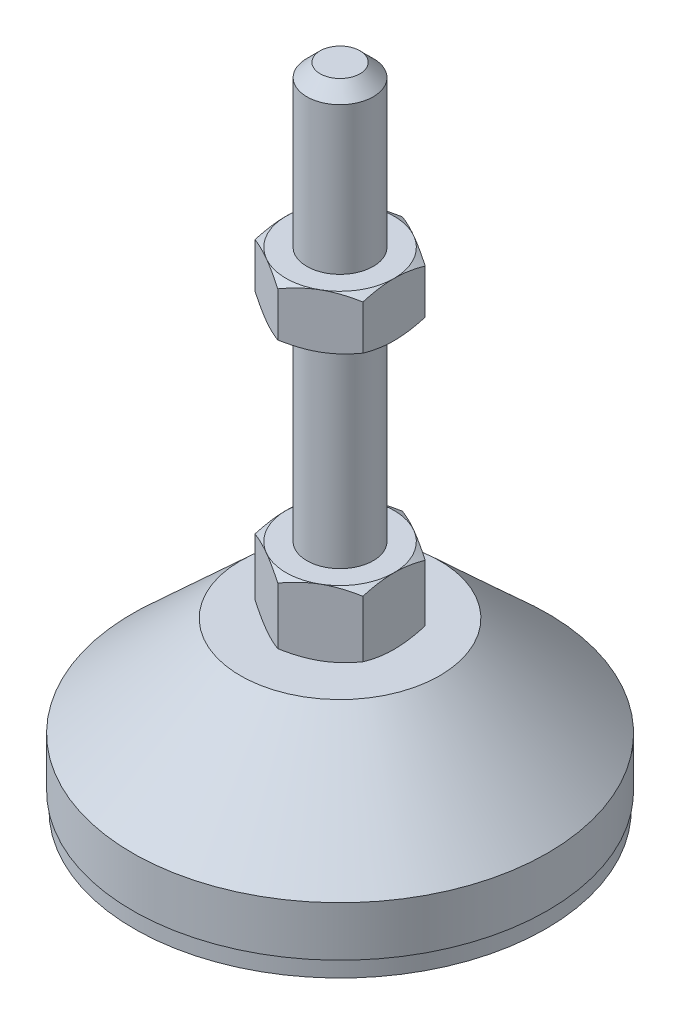
SolidWorks part; units mm, degrees
ref_plane "Спереди" through (0, 0, 0) normal (0, 0, 1) x (1, 0, 0)
ref_plane "Сверху" through (0, 0, 0) normal (0, 1, 0) x (1, 0, 0)
ref_plane "Справа" through (0, 0, 0) normal (1, 0, 0) x (0, 0, -1)
sketch "Эскиз1" plane through (0, 0, 0) normal (0, 0, 1) x (1, 0, 0)
  line L0 (0, 0) -> (-24.8, 0)
  line L1 (-24.8, 0) -> (-24.8, 2)
  line L2 (-24.8, 2) -> (-25, 2)
  line L3 (-25, 2) -> (-25, 8)
  line L4 (-25, 8) -> (-12, 20)
  line L5 (-12, 20) -> (-4, 20)
  line L12 (-4, 28) -> (-4, 76.4)
  line L13 (-4, 76.4) -> (-2.4, 78)
  line L14 (-2.4, 78) -> (0, 78)
  line L15 (0, 78) -> (0, 0) construction
  line L16 (-4, 20) -> (0, 20) construction
  line L17 (0, 0) -> (0, 78)
  line L18 (0, 0) -> (0, -7.9595) construction
  line L19 (-4, 28) -> (-4, 20)
  point P8 (-4, 52.2)
  point P23 (-8, 20)
  dimension "D1" = 8
  dimension "D2" = 20
  dimension "D3" = 8
  dimension "D4" = 50
  dimension "D5" = 4
  dimension "D6" = 1.6
  dimension "D7" = 45
  dimension "D8" = 24
  dimension "D9" = 2
  dimension "D10" = 50
  dimension "D11" = 6
  dimension "D12" = 0.2
revolve "Повернуть1" add sketch "Эскиз1" angle 360 about L17
sketch "Эскиз2" plane through (0, 20, 0) normal (0, 1, 0) x (1, 0, 0)
  line L1 (0, 7.5056) -> (-6.5, 3.7528)
  line L2 (-6.5, 3.7528) -> (-6.5, -3.7528)
  line L3 (-6.5, -3.7528) -> (0, -7.5056)
  line L4 (0, -7.5056) -> (6.5, -3.7528)
  line L5 (6.5, -3.7528) -> (6.5, 3.7528)
  line L6 (6.5, 3.7528) -> (0, 7.5056)
  circle A0 centre (0, 0) radius 6.5 construction
  dimension "D1" = 13
extrude "Бобышка-Вытянуть1" add sketch "Эскиз2" along normal up to vertex (8 mm away) up to point (-4, 28, 0)
ref_plane "Плоскость1" through (0, 52.2, 0) normal (0, 1, 0) x (1, 0, 0)
sketch "Эскиз3" plane through (0, 52.2, 0) normal (0, 1, 0) x (1, 0, 0)
  line L6 (6.5, 3.7528) -> (0, 7.5056)
  line L7 (0, 7.5056) -> (-6.5, 3.7528)
  line L8 (-6.5, 3.7528) -> (-6.5, -3.7528)
  line L9 (-6.5, -3.7528) -> (0, -7.5056)
  line L10 (0, -7.5056) -> (6.5, -3.7528)
  line L11 (6.5, -3.7528) -> (6.5, 3.7528)
  line L12 (6.5, 3.7528) -> (0, 7.5056)
  line L13 (0, 7.5056) -> (-6.5, 3.7528)
  line L14 (-6.5, 3.7528) -> (-6.5, -3.7528)
  line L15 (-6.5, -3.7528) -> (0, -7.5056)
  line L16 (0, -7.5056) -> (6.5, -3.7528)
  line L17 (6.5, -3.7528) -> (6.5, 3.7528)
  dimension "D1" = 0
extrude "Бобышка-Вытянуть2" add sketch "Эскиз3" along normal blind 6.5
sketch "Эскиз4" plane through (0, 0, 0) normal (0, 0, 1) x (1, 0, 0)
  line L0 (-6.5, 58.7) -> (-12.1292, 55.45)
  line L1 (-12.1292, 55.45) -> (-12.1292, 58.7)
  line L2 (-12.1292, 58.7) -> (-6.5, 58.7)
  line L3 (-12.1292, 55.45) -> (-6.5, 52.2)
  line L4 (50, 52.2) -> (-50, 52.2) construction
  line L5 (-6.5, 52.2) -> (-12.1292, 52.2)
  line L6 (-12.1292, 52.2) -> (-12.1292, 55.45)
  line L7 (-6.5, 58.7) -> (-6.5, 52.2) construction
  line L8 (-6.5, 28) -> (-13.4282, 28)
  line L9 (-13.4282, 28) -> (-13.4282, 24)
  line L10 (-13.4282, 24) -> (-6.5, 28)
  line L11 (-6.5, 20) -> (-13.4282, 24)
  line L12 (-13.4282, 24) -> (-13.4282, 20)
  line L13 (-13.4282, 20) -> (-6.5, 20)
  line L14 (0, 78) -> (0, 96.3793) construction
  dimension "D1" = 30
  dimension "D2" = 30
revolve "Вырез-Повернуть2" cut sketch "Эскиз4" angle 360 about L14
